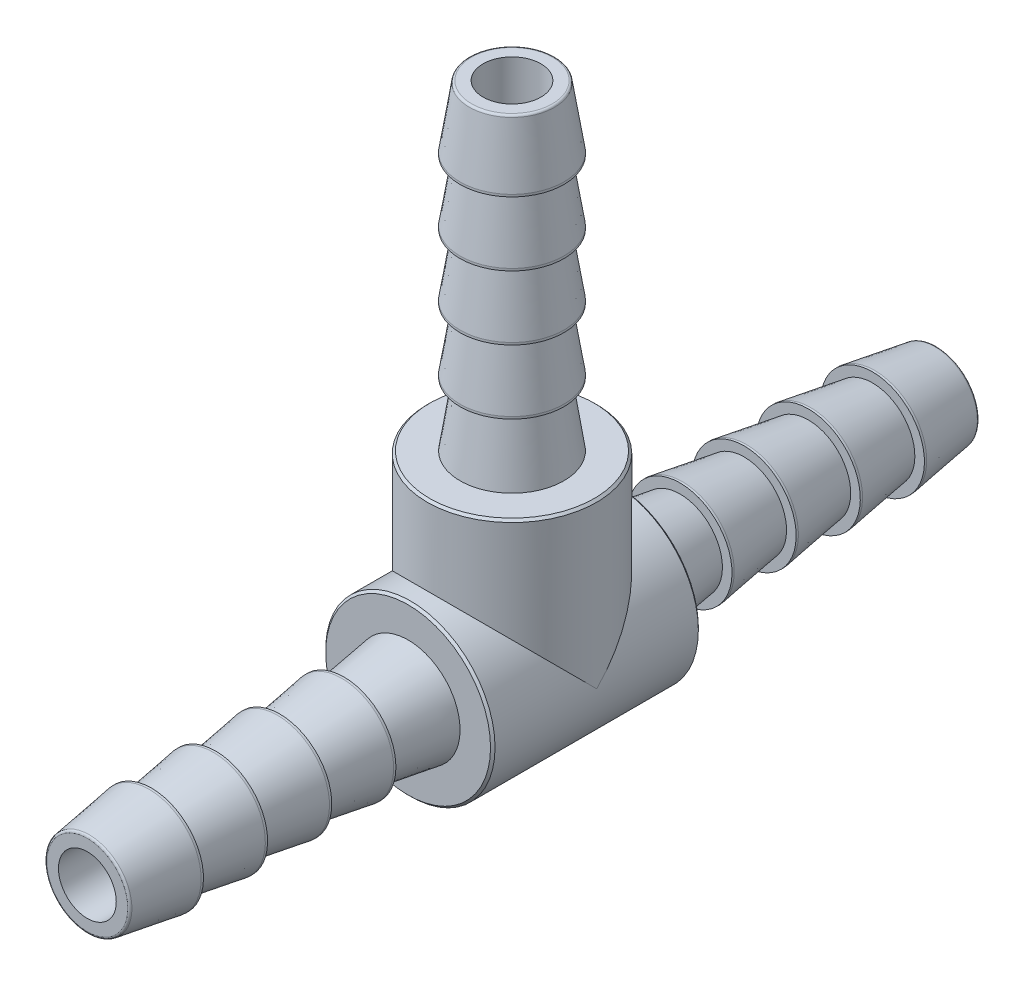
SolidWorks part; units mm, degrees
ref_plane "Front Plane" through (0, 0, 0) normal (0, 0, 1) x (1, 0, 0)
ref_plane "Top Plane" through (0, 0, 0) normal (0, 1, 0) x (1, 0, 0)
ref_plane "Right Plane" through (0, 0, 0) normal (1, 0, 0) x (0, 0, -1)
sketch "Sketch1" plane through (0, 0, 0) normal (1, 0, 0) x (0, 0, -1)
  line L0 (-23.876, 0) -> (23.876, 0) construction
  line L2 (-1.6256, 27.2415) -> (1.6256, 27.2415) construction
  line L3 (-23.876, 2.3813) -> (-23.876, -2.3813) construction
  line L5 (0, 4.7625) -> (0, -4.7625) construction
  line L6 (-23.876, 1.6256) -> (-23.876, -1.6256) construction
  line L7 (-23.876, 2.921) -> (-23.876, -2.921) construction
  line L8 (-2.3813, 27.2415) -> (2.3813, 27.2415) construction
  line L10 (-2.921, 27.2415) -> (2.921, 27.2415) construction
  line L11 (-5.842, 4.7625) -> (-5.842, -4.7625) construction
  line L12 (-4.7625, 9.2075) -> (4.7625, 9.2075) construction
  line L13 (4.7625, 9.2075) -> (4.7625, -4.7625) construction
  line L14 (0, 0) -> (0, 27.2415) construction
  line L15 (-5.842, -4.7625) -> (4.7625, -4.7625) construction
  line L16 (23.876, 2.921) -> (23.876, -2.921) construction
  line L17 (23.876, 1.6256) -> (23.876, -1.6256) construction
  line L18 (23.876, 2.3813) -> (23.876, -2.3813) construction
  line L19 (5.842, 4.7625) -> (5.842, -4.7625) construction
  point P1 (-5.842, 0)
  point P32 (0, 9.2075)
sketch "Sketch2" plane through (0, 0, 0) normal (1, 0, 0) x (0, 0, -1)
  line L1 (-23.876, 0) -> (-23.876, 4.7625)
  line L2 (0, 0) -> (0, 4.7625) construction
  line L3 (-23.876, 4.7625) -> (23.876, 4.7625)
  line L5 (23.876, 0) -> (23.876, 4.7625)
  line L9 (-23.876, 0) -> (0, 0) construction
  line L12 (23.876, 0) -> (-23.876, 0)
revolve "Revolve1" add sketch "Sketch2" angle 360 about L9
sketch "Sketch3" plane through (0, 0, 0) normal (1, 0, 0) x (0, 0, -1)
  line L0 (-23.876, 4.7625) -> (-23.876, 2.3813)
  line L1 (-23.876, 4.7625) -> (-5.842, 4.7625)
  line L2 (-23.876, 2.3813) -> (-9.4488, 2.3813)
  line L3 (-23.876, 0) -> (0, 0) construction
  line L4 (-5.842, 4.7625) -> (-5.842, -4.7625) construction
  line L5 (-23.876, 2.921) -> (-23.876, -2.921) construction
  line L6 (-5.842, 2.921) -> (-9.4488, 2.3813)
  line L7 (0, 0) -> (0, 4.7625) construction
  line L12 (-5.842, 2.921) -> (-5.842, 4.7625)
  dimension "D1" = 3.6068
revolve "Cut-Revolve1" cut sketch "Sketch3" angle 360 about L3
sketch "Sketch4" plane through (0, 0, 0) normal (1, 0, 0) x (0, 0, -1)
  line L0 (-5.842, 0) -> (-23.876, 0) construction
  line L1 (-23.876, 2.3813) -> (-23.876, -2.3813) construction
  line L2 (-20.2692, 2.921) -> (-20.3962, 2.921)
  line L4 (-20.2692, 2.3813) -> (-20.2692, 2.921)
  line L5 (-20.3962, 2.921) -> (-23.876, 2.3813)
  line L7 (-20.2692, 2.3813) -> (-23.876, 2.3813)
  line L8 (-9.4488, 2.3813) -> (-23.876, 2.3813) construction
  dimension "D2" = 3.6068
  dimension "D1" = 0.127
revolve "Revolve2" add sketch "Sketch4" angle 360 about L0
pattern_linear "LPattern1" count 4 spacing 3.6068 along (0, 0, -1) of "Revolve2"
mirror "Mirror1" about plane through (0, 0, 0) normal (0, 0, 1) of "Cut-Revolve1", "Revolve2", "LPattern1"
sketch "Sketch6" plane through (0, 0, 0) normal (1, 0, 0) x (0, 0, -1)
  line L0 (0, 0) -> (0, 27.2415) construction
  line L1 (0, 0) -> (-4.7625, 0)
  line L2 (0, 0) -> (0, 27.2415)
  line L3 (0, 27.2415) -> (-4.7625, 27.2415)
  line L4 (-4.7625, 0) -> (-4.7625, 27.2415)
revolve "Revolve3" add sketch "Sketch6" angle 360 about L0
sketch "Sketch7" plane through (0, 0, 0) normal (1, 0, 0) x (0, 0, -1)
  line L0 (-2.921, 9.2075) -> (-2.3812, 12.8143)
  line L1 (-2.3813, 27.2415) -> (-4.7625, 27.2415)
  line L2 (-2.3813, 27.2415) -> (-2.3812, 12.8143)
  line L3 (-2.921, 9.2075) -> (-4.7625, 9.2075)
  line L4 (-4.7625, 27.2415) -> (-4.7625, 9.2075)
  line L5 (0, 0) -> (0, 27.2415) construction
  dimension "D1" = 3.6068
revolve "Cut-Revolve3" cut sketch "Sketch7" angle 360 about L5
sketch "Sketch8" plane through (0, 0, 0) normal (1, 0, 0) x (0, 0, -1)
  line L0 (-2.3813, 27.2415) -> (-2.921, 23.7617)
  line L1 (-2.921, 23.6347) -> (-2.3813, 23.6347)
  line L2 (-2.3813, 23.6347) -> (-2.3813, 27.2415)
  line L4 (0, 27.2415) -> (0, 0) construction
  line L5 (-1.6256, 27.2415) -> (1.6256, 27.2415) construction
  line L6 (-2.921, 23.7617) -> (-2.921, 23.6347)
  dimension "D2" = 3.6068
  dimension "D1" = 0.127
revolve "Revolve4" add sketch "Sketch8" angle 360 about L4
pattern_linear "LPattern2" count 4 spacing 3.6068 along (0, -1, 0) of "Revolve4"
sketch "Sketch5" plane through (0, 0, 0) normal (1, 0, 0) x (0, 0, -1)
  line L0 (0, 4.7625) -> (0, -4.7625) construction
  line L1 (-23.876, 1.6256) -> (0, 1.6256)
  line L2 (-23.876, 1.6256) -> (-23.876, 0)
  line L3 (-23.876, 0) -> (1.6256, 0)
  arc A0 (1.6256, 0) -> (0, 1.6256) centre (0, 0) ccw
revolve "Cut-Revolve2" cut sketch "Sketch5" angle 360 about L3
sketch "Sketch9" plane through (0, 0, 0) normal (1, 0, 0) x (0, 0, -1)
  line L0 (0, 27.2415) -> (0, 0) construction
  line L1 (-1.6256, 27.2415) -> (0, 27.2415)
  line L2 (-1.6256, 27.2415) -> (-1.6256, 0)
  line L3 (-1.6256, 0) -> (0, 0)
  line L4 (0, 27.2415) -> (0, 0)
revolve "Cut-Revolve4" cut sketch "Sketch9" angle 360 about L0
chamfer "Chamfer1" distance 0.127 angle 45 3 edges at (4.7625, 0, 5.842) (4.7625, 0, -5.842) (0, 9.2075, -4.7625)
fillet "Fillet1" radius 0.127 3 edges at (0, 2.3813, 23.876) (2.3813, 0, -23.876) (0, 27.2415, -2.3813)
equation "\"Barb End Length2@Sketch1\" = \"Barb End Length@Sketch1\""
equation "\"D2@Sketch4\" = \"Barb End Length@Sketch1\" /  ( \"No. of Barbs@LPattern1\" + 1 ) "
equation "\"D1@Sketch3\" = \"D2@Sketch4\""
equation "\"D3@LPattern1\" = \"D2@Sketch4\""
equation "\"No. of Barbs2@LPattern2\" = \"No. of Barbs@LPattern1\""
equation "\"D2@Sketch8\" = \"Barb End Length2@Sketch1\" /  ( \"No. of Barbs2@LPattern2\" + 1 ) "
equation "\"D1@Sketch7\" = \"D2@Sketch8\""
equation "\"D3@LPattern2\" = \"D2@Sketch8\""
